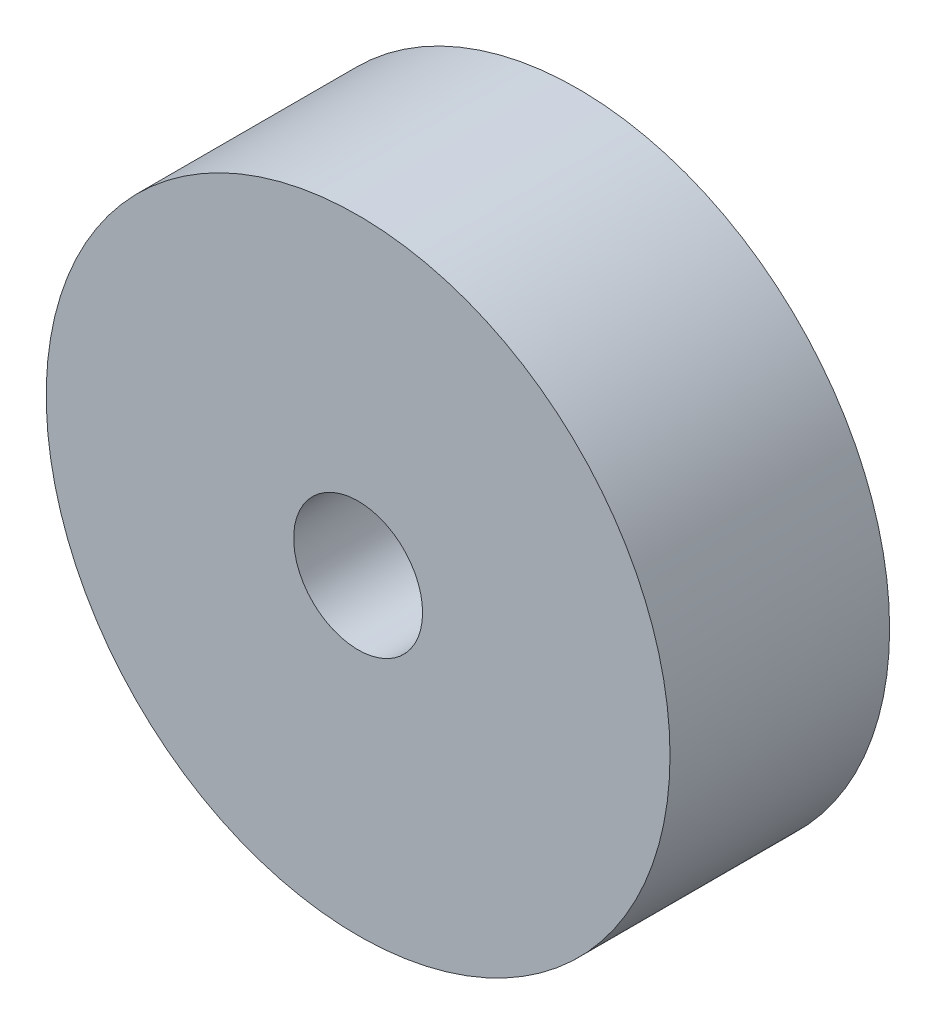
SolidWorks part; units mm, degrees
ref_plane "Front Plane" through (0, 0, 0) normal (0, 0, 1) x (1, 0, 0)
ref_plane "Top Plane" through (0, 0, 0) normal (0, 1, 0) x (1, 0, 0)
ref_plane "Right Plane" through (0, 0, 0) normal (1, 0, 0) x (0, 0, -1)
sketch "Sketch1" plane through (0, 0, 0) normal (0, 0, 1) x (1, 0, 0)
  circle A0 centre (0, 0) radius 37.5
  circle A1 centre (0, 0) radius 7.75
  dimension "D1" = 75
  dimension "D2" = 15.5
extrude "Boss-Extrude1" add sketch "Sketch1" along normal blind 26.4
